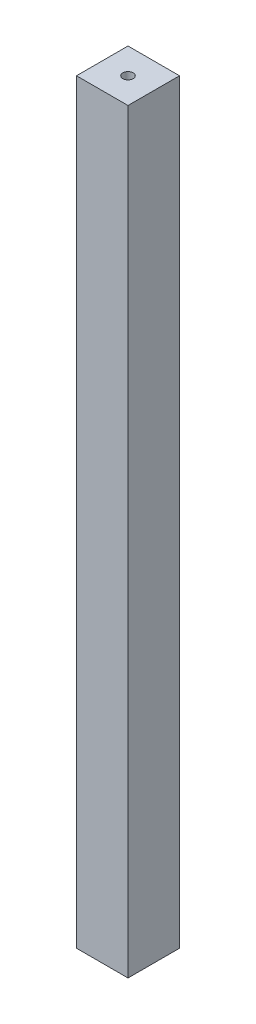
SolidWorks part; units mm, degrees
ref_plane "Front Plane" through (0, 0, 0) normal (0, 0, 1) x (1, 0, 0)
ref_plane "Top Plane" through (0, 0, 0) normal (0, 1, 0) x (1, 0, 0)
ref_plane "Right Plane" through (0, 0, 0) normal (1, 0, 0) x (0, 0, -1)
sketch "Sketch1" plane through (0, 0, 0) normal (0, 1, 0) x (1, 0, 0)
  line L0 (0, -8.25) -> (0, 8.25) construction
  line L1 (-7.5, 7.5) -> (7.5, 7.5)
  line L2 (-7.5, 7.5) -> (-7.5, -7.5)
  line L3 (-7.5, -7.5) -> (7.5, -7.5)
  line L4 (7.5, 7.5) -> (7.5, -7.5)
  line L5 (-8.25, 0) -> (8.25, 0) construction
  circle A0 centre (0, 0) radius 1.5
  dimension "D5" = 3
  dimension "D1" = 15
  dimension "D2" = 15
  dimension "D3" = 7.5
  dimension "D4" = 7.5
extrude "Boss-Extrude1" add sketch "Sketch1" along normal blind 220
